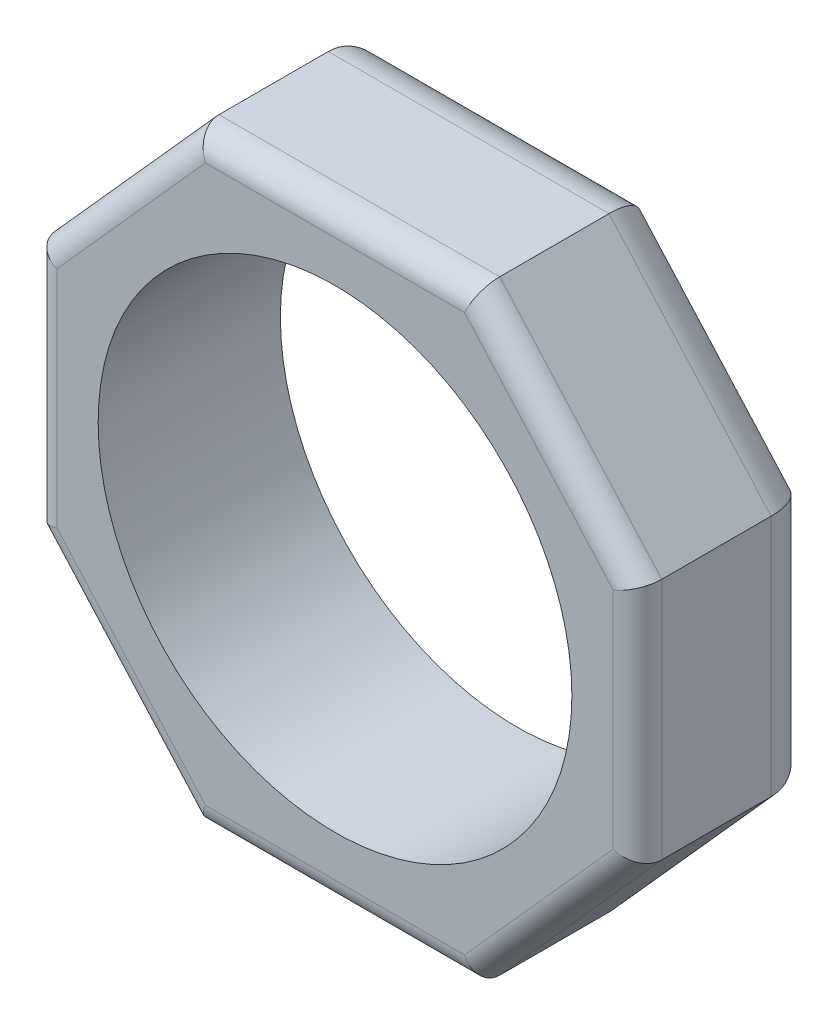
SolidWorks part; units mm, degrees
material "Zinc AC41A Alloy, As Cast"
ref_plane "Front Plane" through (0, 0, 0) normal (0, 0, 1) x (1, 0, 0)
ref_plane "Top Plane" through (0, 0, 0) normal (0, 1, 0) x (1, 0, 0)
ref_plane "Right Plane" through (0, 0, 0) normal (1, 0, 0) x (0, 0, -1)
sketch "Sketch1" plane through (0, 0, 0) normal (0, 0, 1) x (1, 0, 0)
  line L0 (0, 15.8115) -> (0, -15.8115) construction
  line L1 (-7.3398, 15.8115) -> (7.3398, 15.8115)
  line L2 (7.3398, 15.8115) -> (15.8115, 6.35)
  line L3 (15.8115, 6.35) -> (15.8115, -6.35)
  line L4 (15.8115, -6.35) -> (7.3398, -15.8115)
  line L5 (7.3398, -15.8115) -> (-7.3398, -15.8115)
  line L6 (-15.8115, -6.35) -> (-7.3398, -15.8115)
  line L7 (-15.8115, 6.35) -> (-15.8115, -6.35)
  line L8 (-7.3398, 15.8115) -> (-15.8115, 6.35)
  point P3 (0, 0)
  point P4 (15.8115, 0)
  dimension "D1" = 31.623
  dimension "D2" = 31.623
  dimension "D3" = 12.7
  dimension "D4" = 12.7
  dimension "D5" = 12.7
extrude "Boss-Extrude1" add sketch "Sketch1" along normal blind 9.525
fillet "Fillet1" radius 2.54 8 edges at (15.8115, 0, 0) (11.5756, 11.0808, 0) (0, 15.8115, 0) (-11.5756, 11.0807, 0) (-15.8115, 0, 0) (-11.5756, -11.0808, 0) (11.5756, -11.0808, 0) (0, -15.8115, 0)
sketch "Sketch2" plane through (0, 0, 0) normal (0, 0, -1) x (-1, 0, 0)
  circle A0 centre (0, 0) radius 12.3825
  dimension "D1" = 24.765
extrude "Cut-Extrude1" cut sketch "Sketch2" against normal through all
fillet "Fillet2" radius 1.27 8 edges at (0, -15.8115, 9.525) (-11.5756, -11.0808, 9.525) (-15.8115, 0, 9.525) (-11.5756, 11.0807, 9.525) (0, 15.8115, 9.525) (11.5756, 11.0808, 9.525) (15.8115, 0, 9.525) (11.5756, -11.0808, 9.525)
